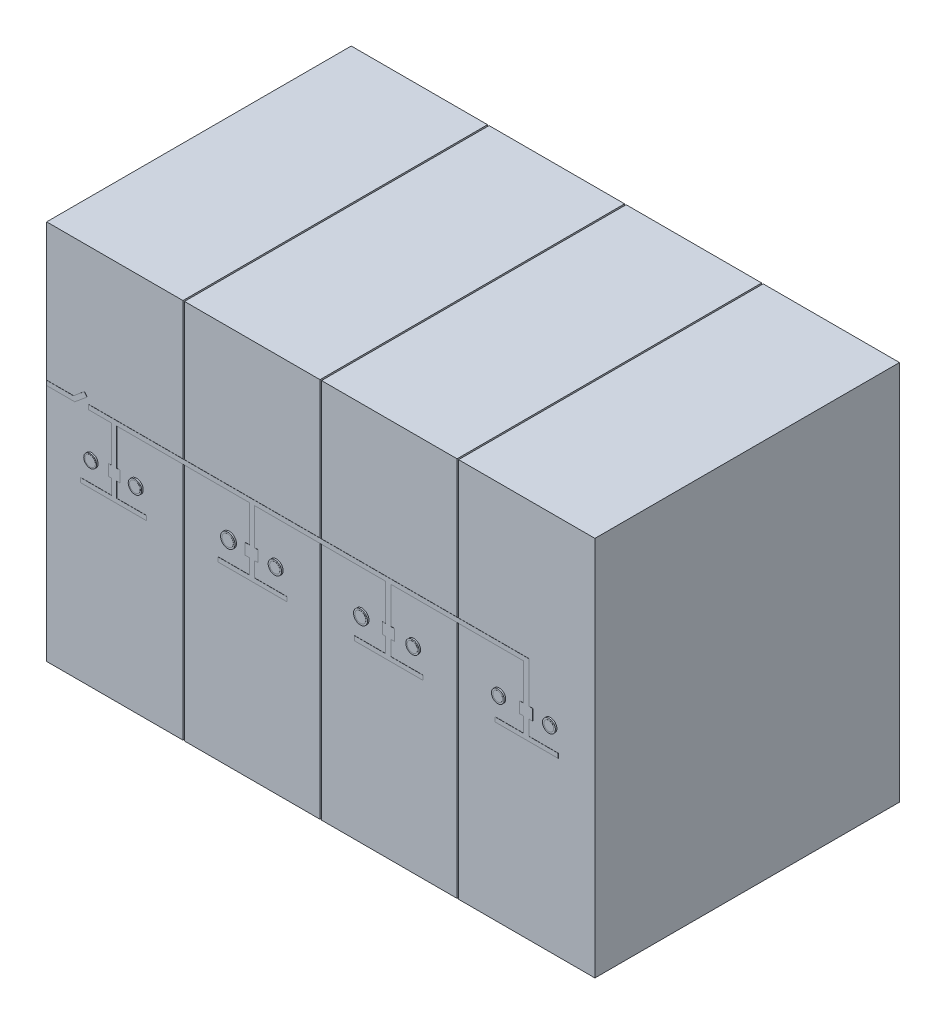
SolidWorks part; units mm, degrees
ref_plane "Alzado" through (0, 0, 0) normal (0, 0, 1) x (1, 0, 0)
ref_plane "Planta" through (0, 0, 0) normal (0, 1, 0) x (1, 0, 0)
ref_plane "Vista lateral" through (0, 0, 0) normal (1, 0, 0) x (0, 0, -1)
sketch "Croquis1" plane through (0, 0, 0) normal (0, 0, 1) x (1, 0, 0)
  line L1 (0, 0) -> (3600, 0)
  line L2 (0, 0) -> (0, 2500)
  line L3 (0, 2500) -> (3600, 2500)
  line L4 (3600, 0) -> (3600, 2500)
  dimension "D1" = 2500
  dimension "D2" = 3600
extrude "Saliente-Extruir1" add sketch "Croquis1" along normal blind 2000
sketch "Croquis3" plane through (0, 0, 2000) normal (0, 0, 1) x (1, 0, 0)
  line L0 (900, 2500) -> (900, 0) construction
  line L1 (3600, 2500) -> (0, 2500) construction
  line L2 (0, 0) -> (3600, 0) construction
  line L3 (0, 2500) -> (0, 0) construction
  line L4 (1800, 2500) -> (1800, 0) construction
  line L5 (2700, 2500) -> (2700, 0) construction
  line L7 (895, 2500) -> (905, 2500)
  line L8 (895, 2500) -> (895, 0)
  line L9 (895, 0) -> (905, 0)
  line L10 (905, 2500) -> (905, 0)
  line L11 (1795, 2500) -> (1805, 2500)
  line L12 (1795, 2500) -> (1795, 0)
  line L13 (1795, 0) -> (1805, 0)
  line L14 (1805, 2500) -> (1805, 0)
  line L15 (2695, 2500) -> (2705, 2500)
  line L16 (2695, 2500) -> (2695, 0)
  line L17 (2695, 0) -> (2705, 0)
  line L18 (2705, 2500) -> (2705, 0)
  dimension "D1" = 900
  dimension "D2" = 900
  dimension "D3" = 900
  dimension "D4" = 5
  dimension "D5" = 5
  dimension "D6" = 5
  dimension "D7" = 5
  dimension "D8" = 5
  dimension "D9" = 5
extrude "Cortar-Extruir1" cut sketch "Croquis3" against normal up to surface (2000 mm away) up to face at (1800, 1250, 0)
sketch "Croquis4" plane through (0, 0, 2000) normal (0, 0, 1) x (1, 0, 0)
  line L0 (0, 2500) -> (0, 0) construction
  line L1 (0, 1600) -> (177.1317, 1600)
  line L2 (0, 1600) -> (0, 1570)
  line L3 (0, 1570) -> (185.7408, 1570)
  line L4 (2262.6706, 1570) -> (3131.3212, 1570)
  line L5 (895, 2500) -> (0, 2500) construction
  line L6 (3168.1971, 1570) -> (3168.1971, 1600)
  line L7 (177.1317, 1600) -> (248.4331, 1659.613)
  line L8 (428.0916, 1570) -> (428.0916, 1329.6964)
  line L9 (460.2557, 1256.8851) -> (483.0878, 1256.8851)
  line L10 (460.2557, 1570) -> (460.2557, 1329.6964)
  line L11 (460.2557, 1570) -> (1331.9799, 1570)
  line L12 (1331.9799, 1570) -> (1331.9799, 1329.6964)
  line L13 (1364.8766, 1329.6964) -> (1388.8424, 1329.6964)
  line L14 (1364.8766, 1570) -> (1364.8766, 1329.6964)
  line L15 (1364.8766, 1570) -> (2226.6417, 1570)
  line L16 (2226.6417, 1570) -> (2226.6417, 1329.6964)
  line L17 (3168.1971, 1329.6964) -> (3192.7276, 1329.6964)
  line L18 (2262.6706, 1570) -> (2262.6706, 1329.6964)
  line L19 (248.4331, 1659.613) -> (266.7378, 1637.7192)
  line L20 (3131.3212, 1570) -> (3131.3212, 1329.6964)
  line L21 (3168.1971, 1158.263) -> (3359.7029, 1158.263)
  line L22 (3168.1971, 1570) -> (3168.1971, 1329.6964)
  line L23 (266.7378, 1637.7192) -> (221.623, 1600)
  line L24 (221.623, 1600) -> (185.7408, 1570)
  line L25 (274.1974, 1600) -> (274.1974, 1570)
  line L26 (274.1974, 1600) -> (3168.1971, 1600)
  line L27 (274.1974, 1570) -> (428.0916, 1570)
  line L28 (460.2557, 1329.6964) -> (483.0878, 1329.6964)
  line L29 (407.8892, 1329.6964) -> (428.0916, 1329.6964)
  line L30 (407.8892, 1329.6964) -> (407.8892, 1256.8851)
  line L31 (407.8892, 1256.8851) -> (428.0916, 1256.8851)
  line L32 (483.0878, 1329.6964) -> (483.0878, 1256.8851)
  line L33 (1364.8766, 1256.8851) -> (1388.8424, 1256.8851)
  line L34 (428.0916, 1256.8851) -> (428.0916, 1158.263)
  line L36 (460.2557, 1256.8851) -> (460.2557, 1158.263)
  line L37 (1304.881, 1329.6964) -> (1331.9799, 1329.6964)
  line L38 (1304.881, 1329.6964) -> (1304.881, 1256.8851)
  line L39 (1304.881, 1256.8851) -> (1331.9799, 1256.8851)
  line L40 (1388.8424, 1329.6964) -> (1388.8424, 1256.8851)
  line L41 (2262.6706, 1329.6964) -> (2284.0989, 1329.6964)
  line L42 (1331.9799, 1256.8851) -> (1331.9799, 1158.263)
  line L43 (460.2557, 1158.263) -> (655.5347, 1158.263)
  line L44 (1364.8766, 1256.8851) -> (1364.8766, 1158.263)
  line L45 (2206.8358, 1329.6964) -> (2226.6417, 1329.6964)
  line L46 (2206.8358, 1329.6964) -> (2206.8358, 1256.8851)
  line L47 (2206.8358, 1256.8851) -> (2226.6417, 1256.8851)
  line L48 (2284.0989, 1329.6964) -> (2284.0989, 1256.8851)
  line L49 (3168.1971, 1256.8851) -> (3192.7276, 1256.8851)
  line L50 (2226.6417, 1256.8851) -> (2226.6417, 1158.263)
  line L51 (1364.8766, 1158.263) -> (1577.8007, 1158.263)
  line L52 (2262.6706, 1256.8851) -> (2262.6706, 1158.263)
  line L53 (2262.6706, 1256.8851) -> (2284.0989, 1256.8851)
  line L54 (2262.6706, 1158.263) -> (2472.729, 1158.263)
  line L55 (3105.8702, 1329.6964) -> (3131.3212, 1329.6964)
  line L56 (3105.8702, 1329.6964) -> (3105.8702, 1256.8851)
  line L57 (3105.8702, 1256.8851) -> (3131.3212, 1256.8851)
  line L58 (3192.7276, 1329.6964) -> (3192.7276, 1256.8851)
  line L60 (3131.3212, 1256.8851) -> (3131.3212, 1158.263)
  line L62 (3168.1971, 1256.8851) -> (3168.1971, 1158.263)
  line L63 (221.623, 1158.263) -> (428.0916, 1158.263)
  line L64 (221.623, 1158.263) -> (221.623, 1129.2586)
  line L65 (221.623, 1129.2586) -> (655.5347, 1129.2586)
  line L66 (655.5347, 1158.263) -> (655.5347, 1129.2586)
  line L67 (1126.8235, 1158.263) -> (1331.9799, 1158.263)
  line L68 (1126.8235, 1158.263) -> (1126.8235, 1129.2586)
  line L69 (1126.8235, 1129.2586) -> (1577.8007, 1129.2586)
  line L70 (1577.8007, 1158.263) -> (1577.8007, 1129.2586)
  line L71 (2021.1788, 1158.263) -> (2226.6417, 1158.263)
  line L72 (2021.1788, 1158.263) -> (2021.1788, 1129.2586)
  line L73 (2021.1788, 1129.2586) -> (2472.729, 1129.2586)
  line L74 (2472.729, 1158.263) -> (2472.729, 1129.2586)
  line L75 (2943.5213, 1158.263) -> (3131.3212, 1158.263)
  line L76 (2943.5213, 1158.263) -> (2943.5213, 1129.2586)
  line L77 (2943.5213, 1129.2586) -> (3359.7029, 1129.2586)
  line L78 (3359.7029, 1158.263) -> (3359.7029, 1129.2586)
  dimension "D1" = 900
  dimension "D2" = 30
extrude "Saliente-Extruir2" add sketch "Croquis4" along normal blind 1
sketch "Croquis5" plane through (0, 0, 2000) normal (0, 0, 1) x (1, 0, 0)
  circle A0 centre (295.4354, 1293.2908) radius 42.0423
  circle A1 centre (589.8306, 1293.2908) radius 44.2274
  circle A2 centre (1199.0901, 1293.2908) radius 47.1619
  circle A3 centre (1508.461, 1293.2908) radius 43.9657
  circle A4 centre (2070.7551, 1293.2908) radius 45.8339
  circle A5 centre (2411.6852, 1293.2908) radius 43.5682
  circle A6 centre (2972.2273, 1293.2908) radius 41.8196
  circle A7 centre (3307.9068, 1293.2908) radius 42.4111
extrude "Saliente-Extruir3" add sketch "Croquis5" along normal blind 10
sketch "Croquis6" plane through (0, 0, 2010) normal (0, 0, 1) x (1, 0, 0)
  circle A0 centre (295.4354, 1293.2908) radius 34.53
  circle A1 centre (589.8306, 1293.2908) radius 35.139
  circle A2 centre (1199.0901, 1293.2908) radius 37.0791
  circle A3 centre (1508.461, 1293.2908) radius 33.4212
  circle A4 centre (2070.7551, 1293.2908) radius 35.5976
  circle A5 centre (2411.6852, 1293.2908) radius 33.9188
  circle A6 centre (2972.2273, 1293.2908) radius 31.9098
  circle A7 centre (3307.9068, 1293.2908) radius 31.6317
extrude "Saliente-Extruir4" add sketch "Croquis6" along normal blind 0.5
